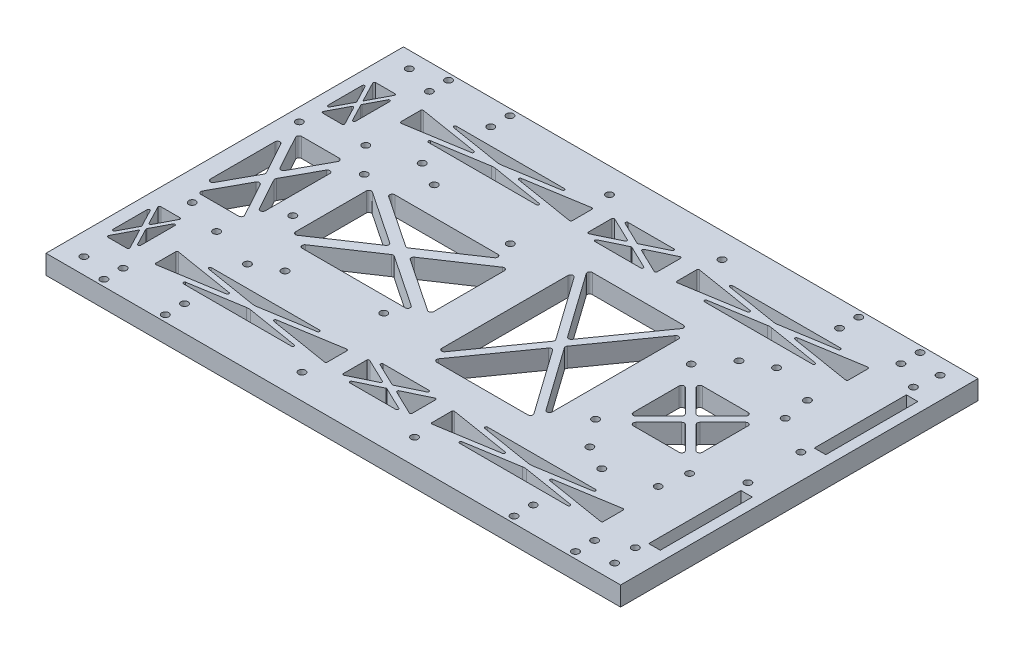
SolidWorks part; units mm, degrees
ref_plane "Front" through (0, 0, 0) normal (0, 0, 1) x (1, 0, 0)
ref_plane "Top" through (0, 0, 0) normal (0, 1, 0) x (1, 0, 0)
ref_plane "Right" through (0, 0, 0) normal (1, 0, 0) x (0, 0, -1)
sketch "arduinoMegaMountingHolesSketch" plane through (0, 0, 0) normal (0, 1, 0) x (1, 0, 0)
  line L1 (0, 0) -> (101.52, 0) construction
  line L2 (0, 0) -> (0, 53.3) construction
  line L3 (0, 53.3) -> (101.52, 53.3) construction
  line L4 (101.52, 0) -> (101.52, 53.3) construction
  circle A0 centre (5.05, 50.76) radius 1.375
  circle A1 centre (87.52, 50.76) radius 1.375
  circle A2 centre (86.29, 2.54) radius 1.375
  circle A3 centre (11.41, 2.54) radius 1.375
  circle A4 centre (35.5, 45.68) radius 1.375
  circle A5 centre (35.5, 17.77) radius 1.375
  dimension "D3" = 5.05
  dimension "D5" = 2.75
  dimension "D1" = 101.52
  dimension "D2" = 53.3
  dimension "D4" = 2.54
  dimension "D6" = 11.41
  dimension "D7" = 2.54
  dimension "D8" = 2.54
  dimension "D9" = 14
  dimension "D10" = 2.54
  dimension "D11" = 15.23
  dimension "D12" = 7.62
  dimension "D13" = 35.5
  dimension "D14" = 35.5
  dimension "D15" = 17.77
sketch "frontMotorMountingHolesSketch" plane through (0, 0, 0) normal (0, 1, 0) x (1, 0, 0)
  line L0 (20.835, 53.3) -> (20.835, 65.05) construction
  line L1 (20.835, 65.05) -> (57.735, 65.05) construction
  line L2 (57.735, 65.05) -> (57.735, 53.3) construction
  line L3 (57.735, 53.3) -> (35.635, 53.3) construction
  line L4 (35.635, 53.3) -> (35.635, 63.3) construction
  line L5 (35.635, 63.3) -> (28.635, 63.3) construction
  line L6 (28.635, 63.3) -> (28.635, 53.3) construction
  line L7 (28.635, 53.3) -> (20.835, 53.3) construction
  line L8 (32.135, 63.3) -> (32.135, 65.05) construction
  line L9 (20.835, 65.05) -> (95.835, 65.05) construction
  line L10 (20.835, 65.05) -> (20.835, 84) construction
  line L11 (20.835, 84) -> (95.835, 84) construction
  line L12 (95.835, 65.05) -> (95.835, 84) construction
  line L13 (0, 0) -> (0, 53.3) construction
  line L14 (26.375, 84) -> (37.895, 84) construction
  line L15 (26.375, 84) -> (26.375, 98.24) construction
  line L16 (26.375, 98.24) -> (37.895, 98.24) construction
  line L17 (37.895, 84) -> (37.895, 98.24) construction
  line L18 (0, 53.3) -> (101.52, 53.3) construction
  line L19 (0, 26.65) -> (101.52, 26.65) construction
  line L20 (0, 98.24) -> (64.27, 98.24) construction
  line L21 (0, 98.24) -> (0, 124.62) construction
  line L22 (0, 124.62) -> (64.27, 124.62) construction
  line L23 (64.27, 98.24) -> (64.27, 124.62) construction
  line L24 (101.52, 0) -> (101.52, 53.3) construction
  line L25 (28.635, 0) -> (20.835, 0) construction
  line L26 (57.735, -11.75) -> (57.735, 0) construction
  line L27 (57.735, 0) -> (35.635, 0) construction
  line L28 (35.635, 0) -> (35.635, -10) construction
  line L29 (32.135, -10) -> (32.135, -11.75) construction
  line L30 (35.635, -10) -> (28.635, -10) construction
  line L31 (20.835, -11.75) -> (57.735, -11.75) construction
  line L32 (20.835, 0) -> (20.835, -11.75) construction
  line L33 (28.635, -10) -> (28.635, 0) construction
  line L34 (20.835, -11.75) -> (20.835, -30.7) construction
  line L35 (20.835, -30.7) -> (95.835, -30.7) construction
  line L36 (95.835, -11.75) -> (95.835, -30.7) construction
  line L37 (20.835, -11.75) -> (95.835, -11.75) construction
  line L38 (37.895, -30.7) -> (37.895, -44.94) construction
  line L39 (26.375, -44.94) -> (37.895, -44.94) construction
  line L40 (26.375, -30.7) -> (26.375, -44.94) construction
  line L41 (0, -44.94) -> (64.27, -44.94) construction
  line L42 (64.27, -44.94) -> (64.27, -71.32) construction
  line L43 (0, -71.32) -> (64.27, -71.32) construction
  line L44 (0, -44.94) -> (0, -71.32) construction
  circle A0 centre (25.985, 55.8) radius 1.375
  circle A1 centre (43.035, 60.8) radius 1.375
  circle A2 centre (52.735, 55.8) radius 1.375
  circle A3 centre (25.985, -2.5) radius 1.375
  circle A4 centre (43.035, -7.5) radius 1.375
  circle A5 centre (52.735, -2.5) radius 1.375
  point P25 (32.135, 98.24)
  point P26 (32.135, 84)
  point P31 (32.135, 98.24)
  dimension "D6" = 2.75
  dimension "D1" = 11.75
  dimension "D2" = 10
  dimension "D3" = 7.8
  dimension "D4" = 22.1
  dimension "D5" = 36.9
  dimension "D7" = 2.65
  dimension "D8" = 2.5
  dimension "D9" = 7.4
  dimension "D10" = 4.25
  dimension "D11" = 5
  dimension "D12" = 2.5
  dimension "D13" = 75
  dimension "D14" = 18.95
  dimension "D15" = 11.52
  dimension "D16" = 14.24
  dimension "D17" = 26.38
  dimension "D18" = 64.27
sketch "L298motorDriverMountingHolesSketch" plane through (0, 0, 0) normal (0, 1, 0) x (1, 0, 0)
  line L0 (182.155, 5.15) -> (182.155, 48.15) construction
  line L1 (160.655, 5.15) -> (203.655, 5.15) construction
  line L2 (160.655, 5.15) -> (160.655, 48.15) construction
  line L3 (160.655, 48.15) -> (203.655, 48.15) construction
  line L4 (203.655, 5.15) -> (203.655, 48.15) construction
  line L5 (160.655, 26.65) -> (203.655, 26.65) construction
  line L6 (166.855, 53.3) -> (166.855, 65.05) construction
  line L7 (166.855, 65.05) -> (203.755, 65.05) construction
  line L8 (203.755, 65.05) -> (203.755, 53.3) construction
  line L9 (203.755, 53.3) -> (195.955, 53.3) construction
  line L10 (195.955, 53.3) -> (195.955, 63.3) construction
  line L11 (195.955, 63.3) -> (188.955, 63.3) construction
  line L12 (188.955, 63.3) -> (188.955, 53.3) construction
  line L13 (188.955, 53.3) -> (166.855, 53.3) construction
  line L15 (101.52, 0) -> (101.52, 53.3) construction
  line L16 (203.755, 65.05) -> (128.755, 65.05) construction
  line L17 (203.755, 65.05) -> (203.755, 84) construction
  line L18 (203.755, 84) -> (128.755, 84) construction
  line L19 (128.755, 65.05) -> (128.755, 84) construction
  line L20 (192.455, 63.3) -> (192.455, 65.05) construction
  line L21 (20.835, 65.05) -> (95.835, 65.05) construction
  line L22 (186.695, 84) -> (198.215, 84) construction
  line L23 (186.695, 84) -> (186.695, 98.24) construction
  line L24 (186.695, 98.24) -> (198.215, 98.24) construction
  line L25 (198.215, 84) -> (198.215, 98.24) construction
  line L26 (160.32, 98.24) -> (224.59, 98.24) construction
  line L27 (160.32, 98.24) -> (160.32, 124.62) construction
  line L28 (160.32, 124.62) -> (224.59, 124.62) construction
  line L29 (224.59, 98.24) -> (224.59, 124.62) construction
  line L30 (224.59, -44.94) -> (224.59, -71.32) construction
  line L31 (160.32, -71.32) -> (224.59, -71.32) construction
  line L32 (160.32, -44.94) -> (160.32, -71.32) construction
  line L33 (160.32, -44.94) -> (224.59, -44.94) construction
  line L34 (186.695, -44.94) -> (198.215, -44.94) construction
  line L35 (186.695, -30.7) -> (186.695, -44.94) construction
  line L36 (198.215, -30.7) -> (198.215, -44.94) construction
  line L37 (203.755, -11.75) -> (203.755, -30.7) construction
  line L38 (203.755, -11.75) -> (128.755, -11.75) construction
  line L39 (128.755, -11.75) -> (128.755, -30.7) construction
  line L40 (203.755, -30.7) -> (128.755, -30.7) construction
  line L41 (203.755, -11.75) -> (203.755, 0) construction
  line L42 (195.955, 0) -> (195.955, -10) construction
  line L43 (195.955, -10) -> (188.955, -10) construction
  line L44 (188.955, -10) -> (188.955, 0) construction
  line L45 (166.855, -11.75) -> (203.755, -11.75) construction
  line L46 (166.855, 0) -> (166.855, -11.75) construction
  line L47 (188.955, 0) -> (166.855, 0) construction
  line L48 (203.755, 0) -> (195.955, 0) construction
  circle A0 centre (163.6057, 45.3859) radius 1.375
  circle A7 centre (163.6057, 8.0064) radius 1.375
  circle A8 centre (200.3475, 45.3859) radius 1.375
  circle A9 centre (200.3475, 8.0064) radius 1.375
  circle A10 centre (171.855, 55.8) radius 1.375
  circle A11 centre (181.555, 60.8) radius 1.375
  circle A12 centre (198.605, 55.8) radius 1.375
  circle A13 centre (198.605, -2.5) radius 1.375
  circle A14 centre (181.555, -7.5) radius 1.375
  circle A15 centre (171.855, -2.5) radius 1.375
  point P4 (160.655, 26.65)
  point P44 (192.455, 84)
  point P49 (192.455, 98.24)
  point P50 (192.455, 98.24)
  dimension "D2" = 2.75
  dimension "D12" = 2.75
  dimension "D1" = 43
  dimension "D3" = 2.7641
  dimension "D4" = 2.9507
  dimension "D5" = 37.3795
  dimension "D6" = 36.7418
  dimension "D7" = 36.7418
  dimension "D8" = 11.75
  dimension "D9" = 36.9
  dimension "D10" = 7
  dimension "D11" = 22.1
  dimension "D13" = 2.65
  dimension "D14" = 2.5
  dimension "D15" = 5
  dimension "D16" = 7.4
  dimension "D17" = 4.25
  dimension "D18" = 10
  dimension "D19" = 18.95
  dimension "D20" = 75
  dimension "D21" = 59.135
  dimension "D22" = 11.52
  dimension "D23" = 14.24
  dimension "D24" = 64.27
  dimension "D25" = 26.38
  dimension "D26" = 20.935
sketch "couplingCollarMountingHolesSketch" plane through (0, 0, 0) normal (0, 1, 0) x (1, 0, 0)
  line L0 (95.835, 65.05) -> (128.755, 65.05) construction
  line L1 (112.295, 124.62) -> (112.295, -71.32) construction
  line L2 (26.375, 98.24) -> (37.895, 98.24) construction
  line L3 (17.135, 84) -> (47.135, 84) construction
  line L4 (17.135, 84) -> (17.135, 96.5) construction
  line L5 (17.135, 96.5) -> (47.135, 96.5) construction
  line L6 (47.135, 84) -> (47.135, 96.5) construction
  line L7 (20.835, 84) -> (95.835, 84) construction
  line L8 (32.135, 96.5) -> (32.135, 84) construction
  line L9 (17.135, 90.25) -> (47.135, 90.25) construction
  line L10 (177.455, 84) -> (177.455, 96.5) construction
  line L11 (207.455, 84) -> (177.455, 84) construction
  line L12 (207.455, 84) -> (207.455, 96.5) construction
  line L13 (207.455, 96.5) -> (177.455, 96.5) construction
  line L14 (0, 26.65) -> (203.655, 26.65) construction
  line L15 (17.135, -30.7) -> (17.135, -43.2) construction
  line L16 (17.135, -43.2) -> (47.135, -43.2) construction
  line L17 (47.135, -30.7) -> (47.135, -43.2) construction
  line L18 (17.135, -30.7) -> (47.135, -30.7) construction
  line L19 (207.455, -30.7) -> (207.455, -43.2) construction
  line L20 (207.455, -43.2) -> (177.455, -43.2) construction
  line L21 (177.455, -30.7) -> (177.455, -43.2) construction
  line L22 (207.455, -30.7) -> (177.455, -30.7) construction
  circle A0 centre (20.135, 86.5) radius 1.375
  circle A1 centre (20.135, 94) radius 1.375
  circle A2 centre (44.135, 86.5) radius 1.375
  circle A3 centre (44.135, 94) radius 1.375
  circle A4 centre (204.455, 86.5) radius 1.375
  circle A5 centre (180.455, 86.5) radius 1.375
  circle A6 centre (180.455, 94) radius 1.375
  circle A7 centre (204.455, 94) radius 1.375
  circle A8 centre (20.135, -33.2) radius 1.375
  circle A9 centre (44.135, -33.2) radius 1.375
  circle A10 centre (44.135, -40.7) radius 1.375
  circle A11 centre (20.135, -40.7) radius 1.375
  circle A12 centre (180.455, -33.2) radius 1.375
  circle A13 centre (204.455, -33.2) radius 1.375
  circle A14 centre (204.455, -40.7) radius 1.375
  circle A15 centre (180.455, -40.7) radius 1.375
  point P6 (112.295, 65.05)
  point P13 (32.135, 84)
  point P16 (32.135, 98.24)
  dimension "D3" = 2.75
  dimension "D1" = 30
  dimension "D2" = 12.5
  dimension "D4" = 2.5
  dimension "D5" = 3
sketch "sideDistanceSensorMountingHolesSketch" plane through (0, 0, 0) normal (0, 1, 0) x (1, 0, 0)
  line L0 (112.295, -43.2) -> (112.295, -30.7) construction
  line L1 (87.295, -43.2) -> (137.295, -43.2) construction
  line L2 (87.295, -43.2) -> (87.295, -30.7) construction
  line L3 (87.295, -30.7) -> (137.295, -30.7) construction
  line L4 (137.295, -43.2) -> (137.295, -30.7) construction
  line L5 (90.795, -43.2) -> (106.795, -43.2) construction
  line L6 (90.795, -43.2) -> (90.795, -55.2) construction
  line L7 (90.795, -55.2) -> (106.795, -55.2) construction
  line L8 (106.795, -43.2) -> (106.795, -55.2) construction
  line L9 (133.795, -43.2) -> (133.795, -55.2) construction
  line L10 (133.795, -55.2) -> (117.795, -55.2) construction
  line L11 (117.795, -43.2) -> (117.795, -55.2) construction
  line L12 (112.295, 124.62) -> (112.295, -71.32) construction
  line L13 (203.755, -30.7) -> (128.755, -30.7) construction
  line L14 (160.655, 26.65) -> (0, 26.65) construction
  line L15 (87.295, 96.5) -> (87.295, 84) construction
  line L16 (87.295, 84) -> (137.295, 84) construction
  line L17 (137.295, 96.5) -> (137.295, 84) construction
  line L18 (133.795, 96.5) -> (133.795, 108.5) construction
  line L19 (133.795, 108.5) -> (117.795, 108.5) construction
  line L20 (90.795, 108.5) -> (106.795, 108.5) construction
  line L21 (90.795, 96.5) -> (90.795, 108.5) construction
  line L22 (106.795, 96.5) -> (106.795, 108.5) construction
  line L23 (112.295, 96.5) -> (112.295, 84) construction
  line L24 (87.295, 96.5) -> (137.295, 96.5) construction
  line L25 (117.795, 96.5) -> (117.795, 108.5) construction
  circle A0 centre (90.295, -33.45) radius 1.375
  circle A2 centre (134.295, -33.45) radius 1.375
  circle A4 centre (90.295, 86.75) radius 1.375
  circle A6 centre (134.295, 86.75) radius 1.375
  point P4 (98.795, -55.2)
  dimension "D6" = 2.75
  dimension "D1" = 12.5
  dimension "D2" = 50
  dimension "D3" = 12
  dimension "D4" = 16
  dimension "D5" = 11.5
  dimension "D7" = 2.75
  dimension "D8" = 3
sketch "topChassisMountingHolesSketch" plane through (0, 0, 0) normal (0, 1, 0) x (1, 0, 0)
  line L0 (17.135, 84) -> (47.135, 84) construction
  line L1 (17.135, 96.5) -> (0, 96.5) construction
  line L2 (17.135, 96.5) -> (17.135, 84) construction
  line L3 (17.135, 84) -> (0, 84) construction
  line L4 (0, 96.5) -> (0, 84) construction
  line L5 (0, 98.24) -> (0, 124.62) construction
  line L6 (8.5675, 84) -> (8.5675, 96.5) construction
  line L7 (0, 26.65) -> (203.655, 26.65) construction
  line L8 (112.295, -71.32) -> (112.295, 124.62) construction
  line L9 (0, -43.2) -> (0, -30.7) construction
  line L10 (17.135, -43.2) -> (0, -43.2) construction
  line L11 (17.135, -43.2) -> (17.135, -30.7) construction
  line L12 (17.135, -30.7) -> (0, -30.7) construction
  line L13 (207.455, 84) -> (224.59, 84) construction
  line L14 (224.59, 96.5) -> (224.59, 84) construction
  line L15 (207.455, 96.5) -> (224.59, 96.5) construction
  line L16 (207.455, 96.5) -> (207.455, 84) construction
  line L17 (207.455, -43.2) -> (224.59, -43.2) construction
  line L18 (224.59, -43.2) -> (224.59, -30.7) construction
  line L19 (207.455, -30.7) -> (224.59, -30.7) construction
  line L20 (207.455, -43.2) -> (207.455, -30.7) construction
  circle A0 centre (8.5675, 90.25) radius 1.375
  circle A1 centre (8.5675, -36.95) radius 1.375
  circle A2 centre (216.0225, 90.25) radius 1.375
  circle A3 centre (216.0225, -36.95) radius 1.375
  dimension "D1" = 2.75
sketch "rearSensorMountingHolesSketch" plane through (0, 0, 0) normal (0, 1, 0) x (1, 0, 0)
  line L0 (212.09, 59) -> (224.59, 59) construction
  line L1 (212.09, 84) -> (224.59, 84) construction
  line L2 (212.09, 84) -> (212.09, 34) construction
  line L3 (212.09, 34) -> (224.59, 34) construction
  line L4 (224.59, 84) -> (224.59, 34) construction
  line L5 (224.59, 80.5) -> (236.59, 80.5) construction
  line L6 (224.59, 80.5) -> (224.59, 64.5) construction
  line L7 (224.59, 64.5) -> (236.59, 64.5) construction
  line L8 (236.59, 80.5) -> (236.59, 64.5) construction
  line L9 (224.59, 53.5) -> (236.59, 53.5) construction
  line L10 (236.59, 37.5) -> (236.59, 53.5) construction
  line L11 (224.59, 37.5) -> (236.59, 37.5) construction
  line L14 (224.59, 96.5) -> (224.59, 84) construction
  line L15 (207.455, 84) -> (224.59, 84) construction
  line L16 (203.655, 26.65) -> (251.7776, 26.65) construction
  line L17 (224.59, -27.2) -> (236.59, -27.2) construction
  line L18 (236.59, -27.2) -> (236.59, -11.2) construction
  line L19 (224.59, -11.2) -> (236.59, -11.2) construction
  line L20 (224.59, -0.2) -> (236.59, -0.2) construction
  line L21 (236.59, 15.8) -> (236.59, -0.2) construction
  line L22 (224.59, 15.8) -> (236.59, 15.8) construction
  line L23 (224.59, -30.7) -> (224.59, 19.3) construction
  line L24 (212.09, -30.7) -> (212.09, 19.3) construction
  line L25 (212.09, 19.3) -> (224.59, 19.3) construction
  circle A0 centre (214.84, 81) radius 1.375
  circle A3 centre (214.84, 37) radius 1.375
  circle A4 centre (214.84, -27.7) radius 1.375
  circle A6 centre (214.84, 16.3) radius 1.375
  dimension "D6" = 2.75
  dimension "D1" = 12.5
  dimension "D2" = 50
  dimension "D3" = 16
  dimension "D4" = 12
  dimension "D5" = 3.5
  dimension "D7" = 2.75
  dimension "D9" = 3
sketch "Sketch6" plane through (0, 0, 0) normal (0, 1, 0) x (1, 0, 0)
  line L0 (17.135, -43.2) -> (0, -43.2) construction
  line L1 (0, 96.5) -> (224.59, 96.5)
  line L2 (0, 96.5) -> (0, -43.2)
  line L3 (0, -43.2) -> (224.59, -43.2)
  line L4 (224.59, 96.5) -> (224.59, -43.2)
  line L5 (224.59, 96.5) -> (224.59, 84) construction
extrude "chassisBase" add sketch "Sketch6" along normal blind 7.5
extrude "arduinoMegaMountingHoles" cut sketch "arduinoMegaMountingHolesSketch" along normal blind 7.5
extrude "frontMotorMountingHoles" cut sketch "frontMotorMountingHolesSketch" along normal blind 7.5
extrude "L298motorDriverMountingHoles" cut sketch "L298motorDriverMountingHolesSketch" along normal blind 7.5
extrude "couplingCollarMountingHoles" cut sketch "couplingCollarMountingHolesSketch" along normal blind 7.5
extrude "sideDistanceSensorMountingHoles" cut sketch "sideDistanceSensorMountingHolesSketch" along normal blind 7.5
extrude "topChassisMountingHoles" cut sketch "topChassisMountingHolesSketch" along normal blind 7.5
extrude "rearSensorMountingHoles" cut sketch "rearSensorMountingHolesSketch" along normal blind 7.5
sketch "Sketch7" plane through (0, 7.5, 0) normal (0, 1, 0) x (1, 0, 0)
  line L0 (87.295, 84) -> (137.295, 84) construction
  line L1 (95.835, 65.05) -> (128.755, 65.05) construction
  line L2 (95.835, 65.05) -> (95.835, 84) construction
  line L3 (95.835, 84) -> (128.755, 84) construction
  line L4 (168.655, 40.15) -> (195.655, 13.15) construction
  line L5 (168.655, 13.15) -> (195.655, 40.15) construction
  line L6 (170.3621, 36.3216) -> (179.3266, 27.3571)
  line L7 (172.4834, 38.4429) -> (181.4479, 29.4784)
  line L8 (168.655, 13.15) -> (195.655, 13.15)
  line L9 (195.655, 13.15) -> (195.655, 40.15)
  line L10 (195.655, 40.15) -> (168.655, 40.15)
  line L11 (168.655, 40.15) -> (168.655, 13.15)
  line L12 (173.1905, 13.15) -> (191.1195, 13.15)
  line L13 (195.655, 17.6855) -> (195.655, 35.6145)
  line L14 (191.1195, 40.15) -> (173.1905, 40.15)
  line L15 (168.655, 35.6145) -> (168.655, 17.6855)
  line L16 (172.4834, 14.8571) -> (181.4479, 23.8216)
  line L17 (170.3621, 16.9784) -> (179.3266, 25.9429)
  line L18 (169.7157, 41.2107) -> (196.7157, 14.2107) construction
  line L19 (167.5943, 39.0893) -> (194.5943, 12.0893) construction
  line L20 (167.5943, 14.2107) -> (194.5943, 41.2107) construction
  line L21 (169.7157, 12.0893) -> (196.7157, 39.0893) construction
  line L22 (184.9834, 25.9429) -> (193.9479, 16.9784)
  line L23 (184.9834, 27.3571) -> (193.9479, 36.3216)
  line L24 (182.8621, 23.8216) -> (191.8266, 14.8571)
  line L25 (182.8621, 29.4784) -> (191.8266, 38.4429)
  line L26 (0, 26.65) -> (203.655, 26.65) construction
  line L27 (113.2947, -3.75) -> (148.8803, -3.75)
  line L28 (109.52, 1.9801) -> (109.52, 51.3199)
  line L29 (113.2947, 57.05) -> (148.8803, 57.05)
  line L30 (152.655, 1.9801) -> (152.655, 51.3199)
  line L31 (109.52, -3.75) -> (152.655, 57.05) construction
  line L32 (109.52, 57.05) -> (152.655, -3.75) construction
  line L33 (160.655, 5.15) -> (160.655, 48.15) construction
  line L34 (101.52, 0) -> (101.52, 53.3) construction
  line L35 (203.755, 65.05) -> (128.755, 65.05) construction
  line L36 (111.3356, 51.8985) -> (128.8378, 27.2286)
  line L37 (112.4791, -2.1714) -> (130.2719, 22.9081)
  line L38 (112.4791, 55.4714) -> (130.2719, 30.3919)
  line L39 (111.3356, 1.4015) -> (128.8378, 26.0714)
  line L40 (110.7434, 57.9179) -> (153.8784, -2.8821) construction
  line L41 (108.2966, 56.1821) -> (151.4316, -4.6179) construction
  line L42 (108.2966, -2.8821) -> (151.4316, 57.9179) construction
  line L43 (110.7434, -4.6179) -> (153.8784, 56.1821) construction
  line L44 (133.3372, 26.0714) -> (150.8394, 1.4015)
  line L45 (131.9031, 30.3919) -> (149.6959, 55.4714)
  line L46 (131.9031, 22.9081) -> (149.6959, -2.1714)
  line L47 (133.3372, 27.2286) -> (150.8394, 51.8985)
  line L48 (203.755, -11.75) -> (128.755, -11.75) construction
  line L49 (128.755, 65.05) -> (128.755, 84) construction
  line L50 (95.835, 65.05) -> (128.755, 65.05) construction
  line L51 (128.755, 65.05) -> (128.755, 84) construction
  line L52 (95.835, 65.05) -> (95.835, 84) construction
  line L53 (103.3346, 81) -> (121.2554, 81)
  line L54 (125.755, 69.9551) -> (125.755, 79.0949)
  line L55 (112.295, 124.62) -> (112.295, 146.2081) construction
  line L56 (24.835, -15.75) -> (91.835, -26.7) construction
  line L57 (24.835, -26.7) -> (91.835, -15.75) construction
  line L58 (37.1136, -25.7065) -> (57.5285, -22.3701)
  line L59 (24.835, -15.75) -> (24.835, -26.7)
  line L60 (20.835, 65.05) -> (20.835, 84) construction
  line L61 (6.6726, 58.3) -> (14.1624, 58.3)
  line L62 (5, 61.9507) -> (5, 75.3493)
  line L63 (6.6726, 79) -> (14.1624, 79)
  line L64 (15.835, 61.9507) -> (15.835, 75.3493)
  line L65 (5, 58.3) -> (15.835, 79) construction
  line L66 (5, 79) -> (15.835, 58.3) construction
  line L67 (0, 53.3) -> (101.52, 53.3) construction
  line L68 (0, 96.5) -> (0, -43.2) construction
  line L69 (17.135, 84) -> (0, 84) construction
  line L70 (5.943, 75.5812) -> (9.4496, 68.8819)
  line L71 (6.2296, 59.0319) -> (9.9745, 66.1864)
  line L72 (6.2296, 78.2681) -> (10.4175, 70.2673)
  line L73 (5.943, 61.7188) -> (9.4496, 68.4181)
  line L74 (5.6645, 79.3478) -> (16.4995, 58.6478) construction
  line L75 (4.3355, 78.6522) -> (15.1705, 57.9522) construction
  line L76 (4.3355, 58.6478) -> (15.1705, 79.3478) construction
  line L77 (5.6645, 57.9522) -> (16.4995, 78.6522) construction
  line L78 (11.3854, 68.4181) -> (14.892, 61.7188)
  line L79 (10.4175, 70.2673) -> (14.6054, 78.2681)
  line L80 (11.3854, 68.8819) -> (14.892, 75.5812)
  line L81 (10.8605, 66.1864) -> (14.6054, 59.0319)
  line L82 (0, 26.65) -> (-18.9445, 26.65) construction
  line L95 (24.835, -26.7) -> (91.835, -26.7)
  line L96 (91.835, -26.7) -> (91.835, -15.75)
  line L97 (91.835, -15.75) -> (24.835, -15.75)
  line L98 (24.835, -17.3516) -> (24.835, -25.0984)
  line L99 (37.1942, -26.7) -> (79.4758, -26.7)
  line L100 (91.835, -25.0984) -> (91.835, -17.3516)
  line L101 (79.4758, -15.75) -> (37.1942, -15.75)
  line L102 (25.4156, -25.5918) -> (49.1158, -21.7185)
  line L103 (25.4156, -16.8582) -> (49.1158, -20.7315)
  line L104 (37.1136, -16.7435) -> (57.5285, -20.0799)
  line L105 (24.9963, -14.7631) -> (91.9963, -25.7131) construction
  line L106 (24.6737, -16.7369) -> (91.6737, -27.6869) construction
  line L107 (24.6737, -25.7131) -> (91.6737, -14.7631) construction
  line L108 (24.9963, -27.6869) -> (91.9963, -16.7369) construction
  line L109 (59.1415, -20.0799) -> (79.5564, -16.7435)
  line L110 (59.1415, -22.3701) -> (79.5564, -25.7065)
  line L111 (67.5542, -20.7315) -> (91.2544, -16.8582)
  line L112 (67.5542, -21.7185) -> (91.2544, -25.5918)
  line L149 (0, 0) -> (101.52, 0) construction
  line L150 (0, 0) -> (35.5, 0) construction
  line L151 (0, 0) -> (0, 53.3) construction
  line L152 (0, 53.3) -> (35.5, 53.3) construction
  line L153 (35.5, 2.54) -> (35.5, 50.76) construction
  line L154 (10.3967, 46.3) -> (25.1033, 46.3)
  line L155 (28.5, 14.0368) -> (28.5, 39.2632)
  line L156 (10.3967, 7) -> (25.1033, 7)
  line L157 (7, 14.0368) -> (7, 39.2632)
  line L158 (7, 46.3) -> (28.5, 7) construction
  line L159 (7, 7) -> (28.5, 46.3) construction
  line L160 (8.8773, 39.7431) -> (15.7776, 27.1299)
  line L161 (9.5194, 8.4799) -> (16.8727, 21.921)
  line L162 (9.5194, 44.8201) -> (16.8727, 31.379)
  line L163 (8.8773, 13.5569) -> (15.7776, 26.1701)
  line L164 (8.3159, 47.0199) -> (29.8159, 7.7199) construction
  line L165 (5.6841, 45.5801) -> (27.1841, 6.2801) construction
  line L166 (7, 7) -> (7, 46.3) construction
  line L167 (7, 46.3) -> (28.5, 46.3) construction
  line L168 (5.6841, 7.7199) -> (27.1841, 47.0199) construction
  line L169 (28.5, 7) -> (28.5, 46.3) construction
  line L170 (8.3159, 6.2801) -> (29.8159, 45.5801) construction
  line L171 (7, 7) -> (28.5, 7) construction
  line L172 (19.7224, 26.1701) -> (26.6227, 13.5569)
  line L173 (18.6273, 31.379) -> (25.9806, 44.8201)
  line L174 (18.6273, 21.921) -> (25.9806, 8.4799)
  line L175 (19.7224, 27.1299) -> (26.6227, 39.7431)
  line L176 (0, 26.65) -> (101.52, 26.65) construction
  line L177 (35.5, 2.54) -> (101.52, 2.54) construction
  line L178 (35.5, 2.54) -> (35.5, 50.76) construction
  line L179 (35.5, 50.76) -> (101.52, 50.76) construction
  line L180 (101.52, 2.54) -> (101.52, 50.76) construction
  line L181 (41.5, 8.54) -> (95.52, 44.76) construction
  line L182 (41.5, 44.76) -> (95.52, 8.54) construction
  line L183 (35.5, 0) -> (35.5, 53.3) construction
  line L184 (48.3784, 44.76) -> (88.6416, 44.76)
  line L185 (95.52, 12.8224) -> (95.52, 40.4776)
  line L186 (48.3784, 8.54) -> (88.6416, 8.54)
  line L187 (41.5, 12.8224) -> (41.5, 40.4776)
  line L188 (43.0569, 41.3082) -> (63.6799, 27.4806)
  line L189 (47.8215, 10.3706) -> (67.9531, 23.8687)
  line L190 (47.8215, 42.9294) -> (67.9531, 29.4313)
  line L191 (43.0569, 11.9918) -> (63.6799, 25.8194)
  line L192 (42.6138, 46.4212) -> (96.6338, 10.2012) construction
  line L193 (41.5, 44.76) -> (95.52, 44.76) construction
  line L194 (41.5, 8.54) -> (41.5, 44.76) construction
  line L195 (40.3862, 43.0988) -> (94.4062, 6.8788) construction
  line L196 (40.3862, 10.2012) -> (94.4062, 46.4212) construction
  line L197 (41.5, 8.54) -> (95.52, 8.54) construction
  line L198 (42.6138, 6.8788) -> (96.6338, 43.0988) construction
  line L199 (95.52, 8.54) -> (95.52, 44.76) construction
  line L200 (69.0669, 29.4313) -> (89.1985, 42.9294)
  line L201 (73.3401, 25.8194) -> (93.9631, 11.9918)
  line L202 (69.0669, 23.8687) -> (89.1985, 10.3706)
  line L203 (73.3401, 27.4806) -> (93.9631, 41.3082)
  line L204 (103.3346, 68.05) -> (121.2554, 68.05)
  line L205 (98.835, 69.9551) -> (98.835, 79.0949)
  line L206 (98.835, 81) -> (125.755, 68.05) construction
  line L207 (98.835, 68.05) -> (125.755, 81) construction
  line L208 (99.5518, 79.5455) -> (109.0516, 74.9756)
  line L209 (103.1178, 69.0006) -> (112.0782, 73.311)
  line L210 (103.1178, 80.0494) -> (112.0782, 75.739)
  line L211 (99.5518, 69.5045) -> (109.0516, 74.0744)
  line L212 (99.2685, 81.9012) -> (126.1885, 68.9512) construction
  line L213 (98.835, 81) -> (125.755, 81) construction
  line L214 (98.835, 68.05) -> (98.835, 81) construction
  line L215 (98.4015, 80.0988) -> (125.3215, 67.1488) construction
  line L216 (98.4015, 68.9512) -> (125.3215, 81.9012) construction
  line L217 (98.835, 68.05) -> (125.755, 68.05) construction
  line L218 (99.2685, 67.1488) -> (126.1885, 80.0988) construction
  line L219 (125.755, 68.05) -> (125.755, 81) construction
  line L220 (112.5118, 75.739) -> (121.4722, 80.0494)
  line L221 (112.5118, 73.311) -> (121.4722, 69.0006)
  line L222 (115.5384, 74.0744) -> (125.0382, 69.5045)
  line L223 (115.5384, 74.9756) -> (125.0382, 79.5455)
  line L236 (25.4156, 70.1582) -> (49.1158, 74.0315)
  line L237 (25.4156, 78.8918) -> (49.1158, 75.0185)
  line L238 (24.835, 70.6516) -> (24.835, 78.3984)
  line L239 (37.1136, 79.0065) -> (57.5285, 75.6701)
  line L240 (59.1415, 75.6701) -> (79.5564, 79.0065)
  line L241 (37.1942, 80) -> (79.4758, 80)
  line L242 (67.5542, 75.0185) -> (91.2544, 78.8918)
  line L243 (67.5542, 74.0315) -> (91.2544, 70.1582)
  line L244 (91.835, 78.3984) -> (91.835, 70.6516)
  line L245 (59.1415, 73.3799) -> (79.5564, 70.0435)
  line L246 (37.1136, 70.0435) -> (57.5285, 73.3799)
  line L247 (79.4758, 69.05) -> (37.1942, 69.05)
  line L248 (157.0358, -21.7185) -> (133.3356, -25.5918)
  line L249 (157.0358, -20.7315) -> (133.3356, -16.8582)
  line L250 (132.755, -25.0984) -> (132.755, -17.3516)
  line L251 (187.4764, -25.7065) -> (167.0615, -22.3701)
  line L252 (165.4485, -22.3701) -> (145.0336, -25.7065)
  line L253 (187.3958, -26.7) -> (145.1142, -26.7)
  line L254 (199.1744, -16.8582) -> (175.4742, -20.7315)
  line L255 (199.1744, -25.5918) -> (175.4742, -21.7185)
  line L256 (199.755, -17.3516) -> (199.755, -25.0984)
  line L257 (165.4485, -20.0799) -> (145.0336, -16.7435)
  line L258 (187.4764, -16.7435) -> (167.0615, -20.0799)
  line L259 (145.1142, -15.75) -> (187.3958, -15.75)
  line L260 (187.4764, 70.0435) -> (167.0615, 73.3799)
  line L261 (145.1142, 69.05) -> (187.3958, 69.05)
  line L262 (165.4485, 73.3799) -> (145.0336, 70.0435)
  line L263 (157.0358, 74.0315) -> (133.3356, 70.1582)
  line L264 (132.755, 78.3984) -> (132.755, 70.6516)
  line L265 (157.0358, 75.0185) -> (133.3356, 78.8918)
  line L266 (187.3958, 80) -> (145.1142, 80)
  line L267 (165.4485, 75.6701) -> (145.0336, 79.0065)
  line L268 (187.4764, 79.0065) -> (167.0615, 75.6701)
  line L269 (199.755, 70.6516) -> (199.755, 78.3984)
  line L270 (199.1744, 78.8918) -> (175.4742, 75.0185)
  line L271 (199.1744, 70.1582) -> (175.4742, 74.0315)
  line L272 (5, -8.6507) -> (5, -22.0493)
  line L273 (5.943, -22.2812) -> (9.4496, -15.5819)
  line L274 (5.943, -8.4188) -> (9.4496, -15.1181)
  line L275 (6.2296, -5.7319) -> (9.9745, -12.8864)
  line L276 (10.8605, -12.8864) -> (14.6054, -5.7319)
  line L277 (6.6726, -5) -> (14.1624, -5)
  line L278 (11.3854, -15.5819) -> (14.892, -22.2812)
  line L279 (15.835, -8.6507) -> (15.835, -22.0493)
  line L280 (11.3854, -15.1181) -> (14.892, -8.4188)
  line L281 (6.2296, -24.9681) -> (10.4175, -16.9673)
  line L282 (10.4175, -16.9673) -> (14.6054, -24.9681)
  line L283 (6.6726, -25.7) -> (14.1624, -25.7)
  line L284 (115.5384, -20.7744) -> (125.0382, -16.2045)
  line L285 (115.5384, -21.6756) -> (125.0382, -26.2455)
  line L286 (125.755, -16.6551) -> (125.755, -25.7949)
  line L287 (103.1178, -15.7006) -> (112.0782, -20.011)
  line L288 (103.3346, -14.75) -> (121.2554, -14.75)
  line L289 (112.5118, -20.011) -> (121.4722, -15.7006)
  line L290 (99.5518, -16.2045) -> (109.0516, -20.7744)
  line L291 (99.5518, -26.2455) -> (109.0516, -21.6756)
  line L292 (98.835, -16.6551) -> (98.835, -25.7949)
  line L293 (103.1178, -26.7494) -> (112.0782, -22.439)
  line L294 (112.5118, -22.439) -> (121.4722, -26.7494)
  line L295 (103.3346, -27.7) -> (121.2554, -27.7)
  line L296 (212.09, 84) -> (212.09, 34) construction
  line L297 (212.09, 37) -> (224.59, 37) construction
  line L298 (212.09, 37) -> (212.09, 81) construction
  line L299 (212.09, 81) -> (224.59, 81) construction
  line L300 (224.59, 37) -> (224.59, 81) construction
  line L303 (224.59, 84) -> (224.59, 34) construction
  line L304 (216.09, 77) -> (220.59, 77)
  line L305 (220.59, 41) -> (220.59, 77)
  line L306 (216.09, 41) -> (220.59, 41)
  line L307 (216.09, 41) -> (216.09, 77)
  line L308 (216.09, 12.3) -> (216.09, -23.7)
  line L309 (216.09, 12.3) -> (220.59, 12.3)
  line L310 (220.59, 12.3) -> (220.59, -23.7)
  line L311 (216.09, -23.7) -> (220.59, -23.7)
  arc A0 (59.1415, -22.3701) -> (57.5285, -22.3701) centre (58.335, -27.3046) ccw
  arc A1 (59.1415, -20.0799) -> (57.5285, -20.0799) centre (58.335, -15.1454) cw
  arc A2 (79.5564, -25.7065) -> (79.4758, -26.7) centre (79.4758, -26.2) cw
  arc A3 (37.1942, -26.7) -> (37.1136, -25.7065) centre (37.1942, -26.2) cw
  arc A4 (79.5564, -16.7435) -> (79.4758, -15.75) centre (79.4758, -16.25) ccw
  arc A5 (37.1136, -16.7435) -> (37.1942, -15.75) centre (37.1942, -16.25) cw
  arc A6 (25.4156, -16.8582) -> (24.835, -17.3516) centre (25.335, -17.3516) ccw
  arc A7 (25.4156, -25.5918) -> (24.835, -25.0984) centre (25.335, -25.0984) cw
  arc A8 (49.1158, -21.7185) -> (49.1158, -20.7315) centre (49.0352, -21.225) ccw
  arc A9 (67.5542, -20.7315) -> (67.5542, -21.7185) centre (67.6348, -21.225) ccw
  arc A10 (91.835, -17.3516) -> (91.2544, -16.8582) centre (91.335, -17.3516) ccw
  arc A11 (91.2544, -25.5918) -> (91.835, -25.0984) centre (91.335, -25.0984) ccw
  arc A12 (49.1158, 75.0185) -> (49.1158, 74.0315) centre (49.0352, 74.525) cw
  arc A13 (25.4156, 70.1582) -> (24.835, 70.6516) centre (25.335, 70.6516) cw
  arc A14 (25.4156, 78.8918) -> (24.835, 78.3984) centre (25.335, 78.3984) ccw
  arc A15 (59.1415, 75.6701) -> (57.5285, 75.6701) centre (58.335, 80.6046) cw
  arc A16 (79.5564, 79.0065) -> (79.4758, 80) centre (79.4758, 79.5) ccw
  arc A17 (37.1942, 80) -> (37.1136, 79.0065) centre (37.1942, 79.5) ccw
  arc A18 (67.5542, 74.0315) -> (67.5542, 75.0185) centre (67.6348, 74.525) cw
  arc A19 (91.835, 70.6516) -> (91.2544, 70.1582) centre (91.335, 70.6516) cw
  arc A20 (91.2544, 78.8918) -> (91.835, 78.3984) centre (91.335, 78.3984) cw
  arc A21 (59.1415, 73.3799) -> (57.5285, 73.3799) centre (58.335, 68.4454) ccw
  arc A22 (79.5564, 70.0435) -> (79.4758, 69.05) centre (79.4758, 69.55) cw
  arc A23 (37.1136, 70.0435) -> (37.1942, 69.05) centre (37.1942, 69.55) ccw
  arc A24 (157.0358, -20.7315) -> (157.0358, -21.7185) centre (156.9552, -21.225) cw
  arc A25 (132.755, -17.3516) -> (133.3356, -16.8582) centre (133.255, -17.3516) cw
  arc A26 (133.3356, -25.5918) -> (132.755, -25.0984) centre (133.255, -25.0984) cw
  arc A27 (165.4485, -22.3701) -> (167.0615, -22.3701) centre (166.255, -27.3046) cw
  arc A28 (145.0336, -25.7065) -> (145.1142, -26.7) centre (145.1142, -26.2) ccw
  arc A29 (187.3958, -26.7) -> (187.4764, -25.7065) centre (187.3958, -26.2) ccw
  arc A30 (175.4742, -21.7185) -> (175.4742, -20.7315) centre (175.5548, -21.225) cw
  arc A31 (199.1744, -16.8582) -> (199.755, -17.3516) centre (199.255, -17.3516) cw
  arc A32 (199.1744, -25.5918) -> (199.755, -25.0984) centre (199.255, -25.0984) ccw
  arc A33 (165.4485, -20.0799) -> (167.0615, -20.0799) centre (166.255, -15.1454) ccw
  arc A34 (145.0336, -16.7435) -> (145.1142, -15.75) centre (145.1142, -16.25) cw
  arc A35 (187.4764, -16.7435) -> (187.3958, -15.75) centre (187.3958, -16.25) ccw
  arc A36 (165.4485, 73.3799) -> (167.0615, 73.3799) centre (166.255, 68.4454) cw
  arc A37 (187.4764, 70.0435) -> (187.3958, 69.05) centre (187.3958, 69.55) cw
  arc A38 (145.0336, 70.0435) -> (145.1142, 69.05) centre (145.1142, 69.55) ccw
  arc A39 (157.0358, 74.0315) -> (157.0358, 75.0185) centre (156.9552, 74.525) ccw
  arc A40 (132.755, 70.6516) -> (133.3356, 70.1582) centre (133.255, 70.6516) ccw
  arc A41 (133.3356, 78.8918) -> (132.755, 78.3984) centre (133.255, 78.3984) ccw
  arc A42 (187.3958, 80) -> (187.4764, 79.0065) centre (187.3958, 79.5) cw
  arc A43 (145.0336, 79.0065) -> (145.1142, 80) centre (145.1142, 79.5) cw
  arc A44 (165.4485, 75.6701) -> (167.0615, 75.6701) centre (166.255, 80.6046) ccw
  arc A45 (199.1744, 70.1582) -> (199.755, 70.6516) centre (199.255, 70.6516) ccw
  arc A46 (199.1744, 78.8918) -> (199.755, 78.3984) centre (199.255, 78.3984) cw
  arc A47 (175.4742, 75.0185) -> (175.4742, 74.0315) centre (175.5548, 74.525) ccw
  arc A48 (149.6959, 55.4714) -> (148.8803, 57.05) centre (148.8803, 56.05) ccw
  arc A49 (150.8394, 51.8985) -> (152.655, 51.3199) centre (151.655, 51.3199) cw
  arc A50 (150.8394, 1.4015) -> (152.655, 1.9801) centre (151.655, 1.9801) ccw
  arc A51 (133.3372, 26.0714) -> (133.3372, 27.2286) centre (134.1528, 26.65) cw
  arc A52 (130.2719, 30.3919) -> (131.9031, 30.3919) centre (131.0875, 30.9706) ccw
  arc A53 (112.4791, 55.4714) -> (113.2947, 57.05) centre (113.2947, 56.05) cw
  arc A54 (111.3356, 51.8985) -> (109.52, 51.3199) centre (110.52, 51.3199) ccw
  arc A55 (128.8378, 26.0714) -> (128.8378, 27.2286) centre (128.0222, 26.65) ccw
  arc A56 (111.3356, 1.4015) -> (109.52, 1.9801) centre (110.52, 1.9801) cw
  arc A57 (131.9031, 22.9081) -> (130.2719, 22.9081) centre (131.0875, 22.3294) ccw
  arc A58 (149.6959, -2.1714) -> (148.8803, -3.75) centre (148.8803, -2.75) cw
  arc A59 (112.4791, -2.1714) -> (113.2947, -3.75) centre (113.2947, -2.75) ccw
  arc A60 (89.1985, 42.9294) -> (88.6416, 44.76) centre (88.6416, 43.76) ccw
  arc A61 (69.0669, 29.4313) -> (67.9531, 29.4313) centre (68.51, 30.2619) cw
  arc A62 (47.8215, 42.9294) -> (48.3784, 44.76) centre (48.3784, 43.76) cw
  arc A63 (41.5, 40.4776) -> (43.0569, 41.3082) centre (42.5, 40.4776) cw
  arc A64 (43.0569, 11.9918) -> (41.5, 12.8224) centre (42.5, 12.8224) cw
  arc A65 (63.6799, 25.8194) -> (63.6799, 27.4806) centre (63.123, 26.65) ccw
  arc A66 (89.1985, 10.3706) -> (88.6416, 8.54) centre (88.6416, 9.54) cw
  arc A67 (48.3784, 8.54) -> (47.8215, 10.3706) centre (48.3784, 9.54) cw
  arc A68 (69.0669, 23.8687) -> (67.9531, 23.8687) centre (68.51, 23.0381) ccw
  arc A69 (73.3401, 27.4806) -> (73.3401, 25.8194) centre (73.897, 26.65) ccw
  arc A70 (93.9631, 11.9918) -> (95.52, 12.8224) centre (94.52, 12.8224) ccw
  arc A71 (95.52, 40.4776) -> (93.9631, 41.3082) centre (94.52, 40.4776) ccw
  arc A72 (191.1195, 40.15) -> (191.8266, 38.4429) centre (191.1195, 39.15) cw
  arc A73 (181.4479, 29.4784) -> (182.8621, 29.4784) centre (182.155, 30.1855) ccw
  arc A74 (172.4834, 38.4429) -> (173.1905, 40.15) centre (173.1905, 39.15) cw
  arc A75 (170.3621, 36.3216) -> (168.655, 35.6145) centre (169.655, 35.6145) ccw
  arc A76 (179.3266, 27.3571) -> (179.3266, 25.9429) centre (178.6195, 26.65) cw
  arc A77 (170.3621, 16.9784) -> (168.655, 17.6855) centre (169.655, 17.6855) cw
  arc A78 (195.655, 35.6145) -> (193.9479, 36.3216) centre (194.655, 35.6145) ccw
  arc A79 (195.655, 17.6855) -> (193.9479, 16.9784) centre (194.655, 17.6855) cw
  arc A80 (184.9834, 25.9429) -> (184.9834, 27.3571) centre (185.6905, 26.65) cw
  arc A81 (182.8621, 23.8216) -> (181.4479, 23.8216) centre (182.155, 23.1145) ccw
  arc A82 (191.1195, 13.15) -> (191.8266, 14.8571) centre (191.1195, 14.15) ccw
  arc A83 (172.4834, 14.8571) -> (173.1905, 13.15) centre (173.1905, 14.15) ccw
  arc A84 (25.9806, 44.8201) -> (25.1033, 46.3) centre (25.1033, 45.3) ccw
  arc A85 (16.8727, 31.379) -> (18.6273, 31.379) centre (17.75, 31.8589) ccw
  arc A86 (9.5194, 44.8201) -> (10.3967, 46.3) centre (10.3967, 45.3) cw
  arc A87 (8.8773, 39.7431) -> (7, 39.2632) centre (8, 39.2632) ccw
  arc A88 (15.7776, 26.1701) -> (15.7776, 27.1299) centre (14.9003, 26.65) ccw
  arc A89 (8.8773, 13.5569) -> (7, 14.0368) centre (8, 14.0368) cw
  arc A90 (28.5, 39.2632) -> (26.6227, 39.7431) centre (27.5, 39.2632) ccw
  arc A91 (26.6227, 13.5569) -> (28.5, 14.0368) centre (27.5, 14.0368) ccw
  arc A92 (19.7224, 27.1299) -> (19.7224, 26.1701) centre (20.5997, 26.65) ccw
  arc A93 (18.6273, 21.921) -> (16.8727, 21.921) centre (17.75, 21.4411) ccw
  arc A94 (25.1033, 7) -> (25.9806, 8.4799) centre (25.1033, 8) ccw
  arc A95 (10.3967, 7) -> (9.5194, 8.4799) centre (10.3967, 8) cw
  arc A96 (5.943, 61.7188) -> (5, 61.9507) centre (5.5, 61.9507) cw
  arc A97 (9.4496, 68.4181) -> (9.4496, 68.8819) centre (9.0066, 68.65) ccw
  arc A98 (5.943, 75.5812) -> (5, 75.3493) centre (5.5, 75.3493) ccw
  arc A99 (6.2296, 78.2681) -> (6.6726, 79) centre (6.6726, 78.5) cw
  arc A100 (14.6054, 78.2681) -> (14.1624, 79) centre (14.1624, 78.5) ccw
  arc A101 (14.892, 75.5812) -> (15.835, 75.3493) centre (15.335, 75.3493) cw
  arc A102 (14.892, 61.7188) -> (15.835, 61.9507) centre (15.335, 61.9507) ccw
  arc A103 (11.3854, 68.4181) -> (11.3854, 68.8819) centre (11.8284, 68.65) cw
  arc A104 (9.9745, 66.1864) -> (10.8605, 66.1864) centre (10.4175, 65.9545) cw
  arc A105 (14.1624, 58.3) -> (14.6054, 59.0319) centre (14.1624, 58.8) ccw
  arc A106 (6.6726, 58.3) -> (6.2296, 59.0319) centre (6.6726, 58.8) cw
  arc A107 (5.943, -22.2812) -> (5, -22.0493) centre (5.5, -22.0493) cw
  arc A108 (5.943, -8.4188) -> (5, -8.6507) centre (5.5, -8.6507) ccw
  arc A109 (9.4496, -15.1181) -> (9.4496, -15.5819) centre (9.0066, -15.35) cw
  arc A110 (9.9745, -12.8864) -> (10.8605, -12.8864) centre (10.4175, -12.6545) ccw
  arc A111 (14.1624, -5) -> (14.6054, -5.7319) centre (14.1624, -5.5) cw
  arc A112 (6.6726, -5) -> (6.2296, -5.7319) centre (6.6726, -5.5) ccw
  arc A113 (14.892, -22.2812) -> (15.835, -22.0493) centre (15.335, -22.0493) ccw
  arc A114 (14.892, -8.4188) -> (15.835, -8.6507) centre (15.335, -8.6507) cw
  arc A115 (11.3854, -15.1181) -> (11.3854, -15.5819) centre (11.8284, -15.35) ccw
  arc A116 (6.2296, -24.9681) -> (6.6726, -25.7) centre (6.6726, -25.2) ccw
  arc A117 (14.6054, -24.9681) -> (14.1624, -25.7) centre (14.1624, -25.2) cw
  arc A118 (103.3346, 68.05) -> (103.1178, 69.0006) centre (103.3346, 68.55) cw
  arc A119 (121.4722, 69.0006) -> (121.2554, 68.05) centre (121.2554, 68.55) cw
  arc A120 (112.5118, 73.311) -> (112.0782, 73.311) centre (112.295, 72.8605) ccw
  arc A121 (115.5384, 74.0744) -> (115.5384, 74.9756) centre (115.7552, 74.525) cw
  arc A122 (125.0382, 69.5045) -> (125.755, 69.9551) centre (125.255, 69.9551) ccw
  arc A123 (125.755, 79.0949) -> (125.0382, 79.5455) centre (125.255, 79.0949) ccw
  arc A124 (121.4722, 80.0494) -> (121.2554, 81) centre (121.2554, 80.5) ccw
  arc A125 (112.5118, 75.739) -> (112.0782, 75.739) centre (112.295, 76.1895) cw
  arc A126 (103.1178, 80.0494) -> (103.3346, 81) centre (103.3346, 80.5) cw
  arc A127 (98.835, 79.0949) -> (99.5518, 79.5455) centre (99.335, 79.0949) cw
  arc A128 (109.0516, 74.0744) -> (109.0516, 74.9756) centre (108.8348, 74.525) ccw
  arc A129 (99.5518, 69.5045) -> (98.835, 69.9551) centre (99.335, 69.9551) cw
  arc A130 (115.5384, -20.7744) -> (115.5384, -21.6756) centre (115.7552, -21.225) ccw
  arc A131 (125.0382, -16.2045) -> (125.755, -16.6551) centre (125.255, -16.6551) cw
  arc A132 (125.755, -25.7949) -> (125.0382, -26.2455) centre (125.255, -25.7949) cw
  arc A133 (103.3346, -14.75) -> (103.1178, -15.7006) centre (103.3346, -15.25) ccw
  arc A134 (121.4722, -15.7006) -> (121.2554, -14.75) centre (121.2554, -15.25) ccw
  arc A135 (112.5118, -20.011) -> (112.0782, -20.011) centre (112.295, -19.5605) cw
  arc A136 (109.0516, -20.7744) -> (109.0516, -21.6756) centre (108.8348, -21.225) cw
  arc A137 (98.835, -25.7949) -> (99.5518, -26.2455) centre (99.335, -25.7949) ccw
  arc A138 (99.5518, -16.2045) -> (98.835, -16.6551) centre (99.335, -16.6551) ccw
  arc A139 (112.5118, -22.439) -> (112.0782, -22.439) centre (112.295, -22.8895) ccw
  arc A140 (121.4722, -26.7494) -> (121.2554, -27.7) centre (121.2554, -27.2) cw
  arc A141 (103.1178, -26.7494) -> (103.3346, -27.7) centre (103.3346, -27.2) ccw
  point P20 (131.0875, 26.65)
  point P79 (10.4175, 68.65)
  point P199 (68.51, 26.65)
  point P285 (58.335, -22.2383)
  point P288 (58.335, -20.2117)
  point P291 (85.6351, -26.7)
  point P294 (31.0349, -26.7)
  point P297 (85.6351, -15.75)
  point P300 (31.0349, -15.75)
  point P303 (24.835, -16.7633)
  point P306 (24.835, -25.6867)
  point P309 (52.1351, -21.225)
  point P312 (64.5349, -21.225)
  point P315 (91.835, -16.7633)
  point P318 (91.835, -25.6867)
  point P399 (132.9267, 26.65)
  point P402 (131.0875, 29.2423)
  point P411 (109.52, -1.1577)
  point P418 (111.3592, -3.75)
  point P461 (184.2763, 26.65)
  point P472 (17.75, 29.7753)
  point P495 (5, 59.9173)
  point P498 (9.571, 68.65)
  point P501 (5, 77.3827)
  point P504 (5.8465, 79)
  point P507 (14.9885, 79)
  point P510 (15.835, 77.3827)
  point P513 (15.835, 59.9173)
  point P516 (11.264, 68.65)
  point P519 (10.4175, 67.0327)
  point P522 (14.9885, 58.3)
  point P525 (5.8465, 58.3)
  point P550 (101.1418, 68.05)
  point P553 (123.4482, 68.05)
  point P556 (112.295, 73.4153)
  point P559 (114.6018, 74.525)
  point P562 (125.755, 69.1597)
  point P565 (125.755, 79.8903)
  point P568 (123.4482, 81)
  point P571 (112.295, 75.6347)
  point P574 (101.1418, 81)
  point P577 (98.835, 79.8903)
  point P580 (109.9882, 74.525)
  point P583 (98.835, 69.1597)
  dimension "D32" = 5
  dimension "D33" = 0.5
  dimension "D34" = 0.5
  dimension "D35" = 0.5
  dimension "D36" = 1
  dimension "D37" = 1
  dimension "D38" = 1
  dimension "D39" = 1
  dimension "D40" = 0.5
  dimension "D41" = 0.5
  dimension "D6" = 8
  dimension "D7" = 8
  dimension "D8" = 8
  dimension "D11" = 8
  dimension "D12" = 5
  dimension "D13" = 5
  dimension "D14" = 5
  dimension "D15" = 5
  dimension "D1" = 8
  dimension "D2" = 1.5
  dimension "D3" = 1.5
  dimension "D4" = 1.5
  dimension "D5" = 1.5
  dimension "D9" = 1.5
  dimension "D10" = 1.5
  dimension "D16" = 0.75
  dimension "D17" = 0.75
  dimension "D18" = 4
  dimension "D19" = 1
  dimension "D20" = 1
  dimension "D21" = 1
  dimension "D22" = 1
  dimension "D23" = 7
  dimension "D24" = 1.5
  dimension "D25" = 1.5
  dimension "D26" = 6
  dimension "D27" = 2
  dimension "D28" = 2
  dimension "D29" = 3
  dimension "D30" = 1
  dimension "D31" = 1
  dimension "D42" = 4
extrude "weightReduction" cut sketch "Sketch7" against normal through all
